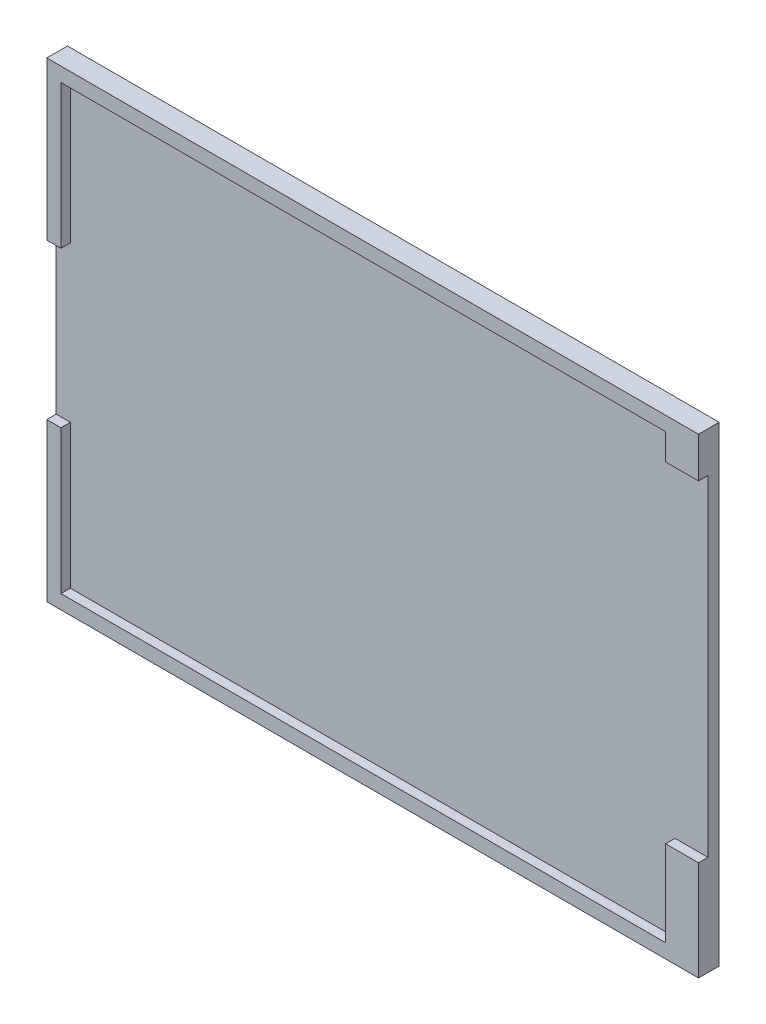
SolidWorks part; units mm, degrees
material "ABS"
ref_plane "Plan de face" through (0, 0, 0) normal (0, 0, 1) x (1, 0, 0)
ref_plane "Plan de dessus" through (0, 0, 0) normal (0, 1, 0) x (1, 0, 0)
ref_plane "Plan de droite" through (0, 0, 0) normal (1, 0, 0) x (0, 0, -1)
sketch "Esquisse1" plane through (0, 0, 0) normal (0, 0, 1) x (1, 0, 0)
  line L1 (-34.6, -25) -> (34.6, -25)
  line L2 (-34.6, -25) -> (-34.6, 25)
  line L3 (-34.6, 25) -> (34.6, 25)
  line L4 (34.6, -25) -> (34.6, 25)
  line L5 (-34.6, -25) -> (34.6, 25) construction
  line L6 (-34.6, 25) -> (34.6, -25) construction
  point P0 (0, 0)
  dimension "D1" = 69.2
  dimension "D2" = 50
extrude "Boss.-Extru.1" add sketch "Esquisse1" along normal blind 2.2
sketch "Esquisse2" plane through (0, 0, 2.2) normal (0, 0, 1) x (1, 0, 0)
  line L0 (-34.6, 0) -> (-34.6, 8.25) construction
  line L1 (-34.6, 25) -> (-34.6, -25) construction
  line L2 (-34.6, 0) -> (-34.6, -8.25) construction
  line L3 (-34.6, -25) -> (-34.6, -23.5) construction
  line L4 (-34.6, -23.5) -> (34.6, -23.5) construction
  line L5 (34.6, -25) -> (34.6, 25) construction
  line L6 (-34.6, -23.5) -> (-33.0954, -23.5) construction
  line L7 (-33.0954, -23.5) -> (-33.0954, 25) construction
  line L8 (34.6, 25) -> (-34.6, 25) construction
  line L9 (-33.0954, 25) -> (-33.0954, 23.4956) construction
  line L10 (-33.0954, 23.4956) -> (34.6, 23.4956) construction
  line L11 (34.6, 23.4956) -> (31.1043, 23.4956) construction
  line L12 (31.1043, 23.4956) -> (31.1043, -23.5) construction
  line L13 (34.6, 25) -> (34.6, 20.7043) construction
  line L14 (34.6, -25) -> (34.6, -14.4043) construction
  line L15 (34.6, 20.7043) -> (31.1043, 20.7043)
  line L16 (31.1043, 20.7043) -> (31.1043, 23.4956)
  line L17 (31.1043, 23.4956) -> (-33.0954, 23.4956)
  line L18 (-33.0954, 23.4956) -> (-33.0954, 8.25)
  line L19 (-33.0954, 8.25) -> (-34.5108, 8.25)
  line L20 (-34.5108, 8.25) -> (-34.6, 8.25)
  line L21 (-34.6, 8.25) -> (-34.6, -8.25)
  line L22 (-34.6, -8.25) -> (-33.0954, -8.25)
  line L23 (-33.0954, -8.25) -> (-33.0954, -23.5)
  line L24 (-33.0954, -23.5) -> (31.1043, -23.5)
  line L25 (31.1043, -23.5) -> (31.1043, -14.4043)
  line L26 (31.1043, -14.4043) -> (34.6, -14.4043)
  line L27 (34.6, -14.4043) -> (34.6, 20.7043)
  dimension "D1" = 8.25
  dimension "D2" = 8.25
  dimension "D3" = 1.5
  dimension "D4" = 4.2957
  dimension "D5" = 10.5957
extrude "Enlèv. mat.-Extru.1" cut sketch "Esquisse2" against normal blind 1
